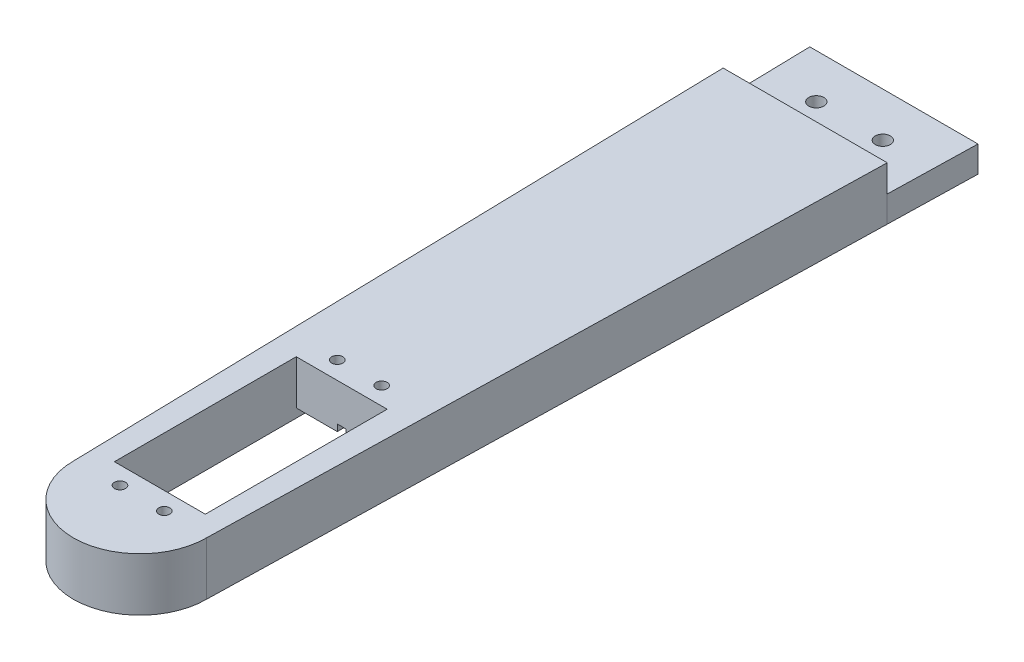
SolidWorks part; units mm, degrees
ref_plane "Front Plane" through (0, 0, 0) normal (0, 0, 1) x (1, 0, 0)
ref_plane "Top Plane" through (0, 0, 0) normal (0, 1, 0) x (1, 0, 0)
ref_plane "Right Plane" through (0, 0, 0) normal (1, 0, 0) x (0, 0, -1)
sketch "Sketch1" plane through (0, 0, 0) normal (0, 1, 0) x (1, 0, 0)
  line L0 (0, 75) -> (0, -75) construction
  line L1 (-18.5, 75) -> (18.5, 75)
  line L2 (-18.5, 75) -> (-15, -75)
  line L3 (18.5, 75) -> (15, -75)
  circle A0 centre (0, -75) radius 15
  point P4 (0, 0)
  point P8 (0, 75)
  dimension "D3" = 30
  dimension "D1" = 37
  dimension "D2" = 150
extrude "Boss-Extrude1" add sketch "Sketch1" along normal blind 12
sketch "Sketch2" plane through (0, 0, 0) normal (0, -1, 0) x (1, 0, 0)
  line L0 (0, -75) -> (0, -95) construction
  line L1 (-18.5, -75) -> (18.5, -75) construction
  line L2 (18.965, -95) -> (-18.965, -95)
  line L3 (-18.965, -95) -> (-18.5, -75)
  line L4 (18.5, -75) -> (18.965, -95)
  line L5 (-18.5, -75) -> (18.5, -75)
  line L8 (-15, 75) -> (-18.5, -75)
  line L9 (-18.5, -75) -> (18.5, -75)
  line L10 (18.5, -75) -> (15, 75)
  line L11 (-15, 75) -> (-18.5, -75)
  line L13 (18.5, -75) -> (15, 75)
  arc A1 (15, 75) -> (-15, 75) centre (0, 75) ccw
  arc A2 (15, 75) -> (-15, 75) centre (0, 75) ccw
  point P8 (0, -95)
  point P11 (-27.6507, -95)
  line M11 (-18.5, -75) -> (18.5, -75)
  dimension "D1" = 20
  dimension "D2" = 37.93
  dimension "D3" = 0
extrude "Boss-Extrude2" add sketch "Sketch2" against normal blind 5.9 contours L5 L0 L2 L4 | L0 L3 L2 M11
sketch "Sketch3" plane through (0, 0, 0) normal (0, -1, 0) x (1, 0, 0)
  line L0 (0, -95) -> (0, -85) construction
  line L1 (18.965, -95) -> (-18.965, -95) construction
  line L2 (7.5, -85) -> (-7.5, -85) construction
  circle A0 centre (-7.5, -85) radius 1.7
  circle A1 centre (7.5, -85) radius 1.7
  point P8 (0, -85)
  dimension "D1" = 10
  dimension "D2" = 15
extrude "Cut-Extrude1" cut sketch "Sketch3" against normal blind 5.9
sketch "Sketch4" plane through (0, 0, 0) normal (0, -1, 0) x (1, 0, 0)
  line L1 (-7.5, -81.7668) -> (-10.3, -83.3834)
  line L2 (-10.3, -83.3834) -> (-10.3, -86.6166)
  line L3 (-10.3, -86.6166) -> (-7.5, -88.2332)
  line L4 (-7.5, -88.2332) -> (-4.7, -86.6166)
  line L5 (-4.7, -86.6166) -> (-4.7, -83.3834)
  line L6 (-4.7, -83.3834) -> (-7.5, -81.7668)
  line L7 (7.5, -81.7668) -> (4.7, -83.3834)
  line L8 (4.7, -83.3834) -> (4.7, -86.6166)
  line L9 (4.7, -86.6166) -> (7.5, -88.2332)
  line L10 (7.5, -88.2332) -> (10.3, -86.6166)
  line L11 (10.3, -86.6166) -> (10.3, -83.3834)
  line L12 (10.3, -83.3834) -> (7.5, -81.7668)
  circle A0 centre (-7.5, -85) radius 2.8 construction
  circle A1 centre (7.5, -85) radius 2.8 construction
extrude "Cut-Extrude2" cut sketch "Sketch4" against normal blind 3
sketch "Sketch5" plane through (0, 0, 0) normal (0, -1, 0) x (1, 0, 0)
  line L0 (0, 90) -> (0, 50) construction
  line L2 (-10.25, 70.5) -> (10.25, 70.5)
  line L3 (-10.25, 70.5) -> (-10.25, 29.5)
  line L4 (-10.25, 29.5) -> (10.25, 29.5)
  line L5 (10.25, 70.5) -> (10.25, 29.5)
  line L6 (-10.25, 70.5) -> (10.25, 29.5) construction
  line L7 (-10.25, 29.5) -> (10.25, 70.5) construction
  arc A0 (15, 75) -> (-15, 75) centre (0, 75) ccw construction
  dimension "D1" = 40
  dimension "D2" = 41
  dimension "D3" = 20.5
extrude "Cut-Extrude3" cut sketch "Sketch5" against normal blind 12
sketch "Sketch6" plane through (0, 0, 0) normal (0, -1, 0) x (1, 0, 0)
  line L0 (-10.25, 50) -> (10.25, 50) construction
  line L1 (-10.25, 70.5) -> (-10.25, 29.5) construction
  line L2 (10.25, 29.5) -> (10.25, 70.5) construction
  line L4 (-10.25, 22.5) -> (10.25, 22.5)
  line L5 (-10.25, 22.5) -> (-10.25, 77.5)
  line L6 (-10.25, 77.5) -> (10.25, 77.5)
  line L7 (10.25, 22.5) -> (10.25, 77.5)
  line L8 (-10.25, 22.5) -> (10.25, 77.5) construction
  line L9 (-10.25, 77.5) -> (10.25, 22.5) construction
  point P6 (0, 50)
  dimension "D1" = 55
extrude "Cut-Extrude4" cut sketch "Sketch6" against normal blind 2
sketch "Sketch7" plane through (0, 2, 0) normal (0, -1, 0) x (1, 0, 0)
  line L0 (0, 70.5) -> (0, 77.5) construction
  line L1 (10.25, 70.5) -> (-10.25, 70.5) construction
  line L2 (10.25, 77.5) -> (-10.25, 77.5) construction
  line L3 (-10.25, 50) -> (10.25, 50) construction
  line L4 (-1, 77.5) -> (1, 77.5)
  line L5 (-1, 77.5) -> (-1, 70.5)
  line L6 (-1, 70.5) -> (1, 70.5)
  line L7 (1, 77.5) -> (1, 70.5)
  line L8 (-1, 77.5) -> (1, 70.5) construction
  line L9 (-1, 70.5) -> (1, 77.5) construction
  line L10 (-10.25, 77.5) -> (-10.25, 22.5) construction
  line L11 (10.25, 22.5) -> (10.25, 77.5) construction
  line L12 (-1, 29.5) -> (1, 22.5) construction
  line L13 (-1, 22.5) -> (1, 29.5) construction
  line L14 (0, 29.5) -> (0, 22.5) construction
  line L15 (1, 22.5) -> (1, 29.5)
  line L16 (-1, 29.5) -> (1, 29.5)
  line L17 (-1, 22.5) -> (-1, 29.5)
  line L18 (-1, 22.5) -> (1, 22.5)
  point P6 (0, 74)
  dimension "D1" = 2
extrude "Cut-Extrude5" cut sketch "Sketch7" against normal blind 1.5
sketch "Sketch8" plane through (0, 2, 0) normal (0, -1, 0) x (1, 0, 0)
  line L0 (0, 70.5) -> (0, 74.5) construction
  line L1 (-1, 70.5) -> (1, 70.5) construction
  line L2 (5, 74.5) -> (-5, 74.5) construction
  line L3 (-10.25, 50) -> (10.25, 50) construction
  line L4 (-10.25, 77.5) -> (-10.25, 22.5) construction
  line L5 (10.25, 22.5) -> (10.25, 77.5) construction
  circle A0 centre (-5, 74.5) radius 1.25
  circle A1 centre (5, 74.5) radius 1.25
  circle A2 centre (5, 25.5) radius 1.25
  circle A3 centre (-5, 25.5) radius 1.25
  point P8 (0, 74.5)
  dimension "D3" = 2.5
  dimension "D1" = 4
  dimension "D2" = 10
extrude "Cut-Extrude6" cut sketch "Sketch8" against normal blind 12
